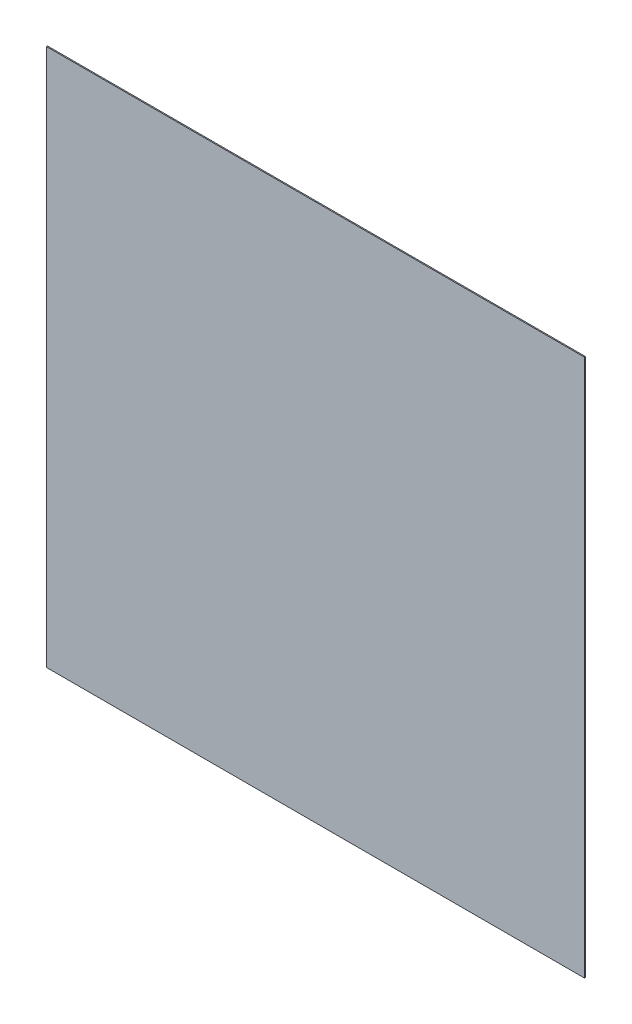
SolidWorks part; units mm, degrees
ref_plane "前视基准面" through (0, 0, 0) normal (0, 0, 1) x (1, 0, 0)
ref_plane "上视基准面" through (0, 0, 0) normal (0, 1, 0) x (1, 0, 0)
ref_plane "右视基准面" through (0, 0, 0) normal (1, 0, 0) x (0, 0, -1)
sketch "草图1" plane through (0, 0, 0) normal (0, 0, 1) x (1, 0, 0)
  line L0 (-74.3628, 41.4094) -> (-74.3628, -4958.5906)
  line L1 (-74.3628, -4958.5906) -> (4925.6372, -4958.5906)
  line L2 (4925.6372, -4958.5906) -> (4925.6372, 41.4094)
  line L3 (4925.6372, 41.4094) -> (-74.3628, 41.4094)
  dimension "D1" = 5000
  dimension "D2" = 5000
extrude "凸台-拉伸1" add sketch "草图1" along normal blind 10
